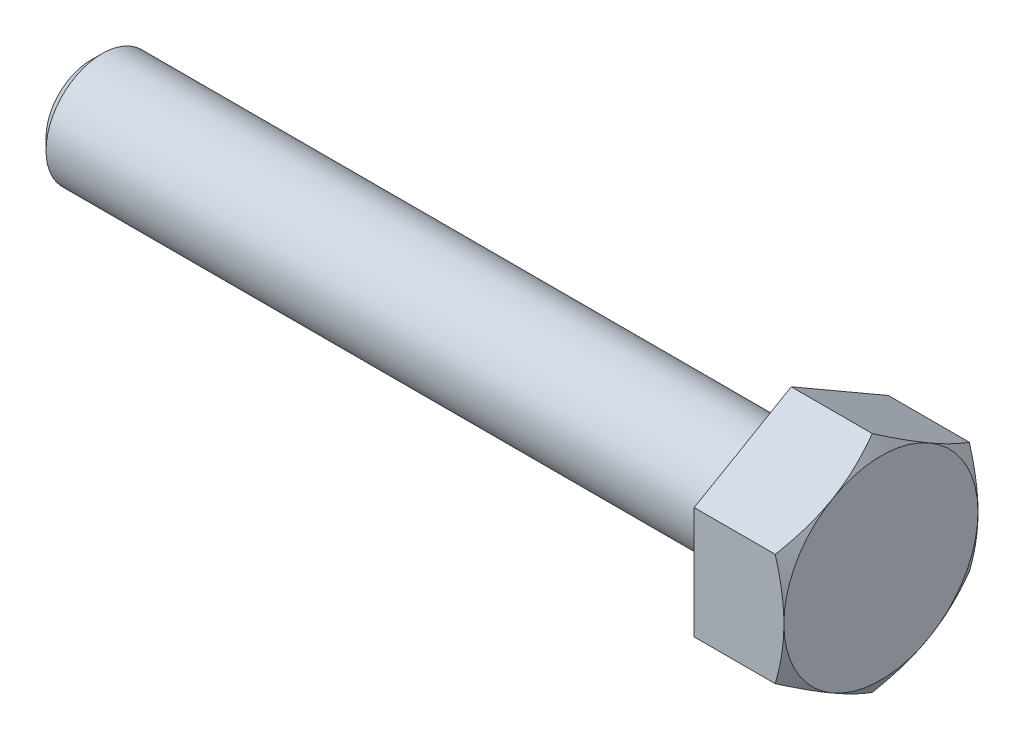
SolidWorks part; units mm, degrees
ref_plane "Front Plane" through (0, 0, 0) normal (0, 0, 1) x (1, 0, 0)
ref_plane "Top Plane" through (0, 0, 0) normal (0, 1, 0) x (1, 0, 0)
ref_plane "Right Plane" through (0, 0, 0) normal (1, 0, 0) x (0, 0, -1)
sketch "Sketch1" plane through (0, 0, 0) normal (1, 0, 0) x (0, 0, -1)
  line L1 (0, 24) -> (-20.7846, 12)
  line L2 (-20.7846, 12) -> (-20.7846, -12)
  line L3 (-20.7846, -12) -> (0, -24)
  line L4 (0, -24) -> (20.7846, -12)
  line L5 (20.7846, -12) -> (20.7846, 12)
  line L6 (20.7846, 12) -> (0, 24)
  dimension "D1" = 24
extrude "Boss-Extrude2" add sketch "Sketch1" along normal blind 19.2
sketch "Sketch3" plane through (0, 0, 0) normal (-1, 0, 0) x (0, 0, 1)
  circle A0 centre (0, 0) radius 12
extrude "Boss-Extrude3" add sketch "Sketch3" along normal blind 150
cosmetic thread "Cosmetic Thread1" parameters "D1"=60, "D2"=20.704
chamfer "Chamfer1" distance 2.4 angle 45 1 edges at (-150, 0, 12)
sketch "Sketch4" plane through (19.2, 0, 0) normal (1, 0, 0) x (0, 0, -1)
  circle A0 centre (0, 0) radius 20.7846 construction
sketch "Sketch5" plane through (19.2, 0, 0) normal (1, 0, 0) x (0, 0, -1)
  circle A0 centre (0, 0) radius 20.7846
extrude "Cut-Extrude1" cut sketch "Sketch5" against normal blind 150 draft 60 flip side to cut
